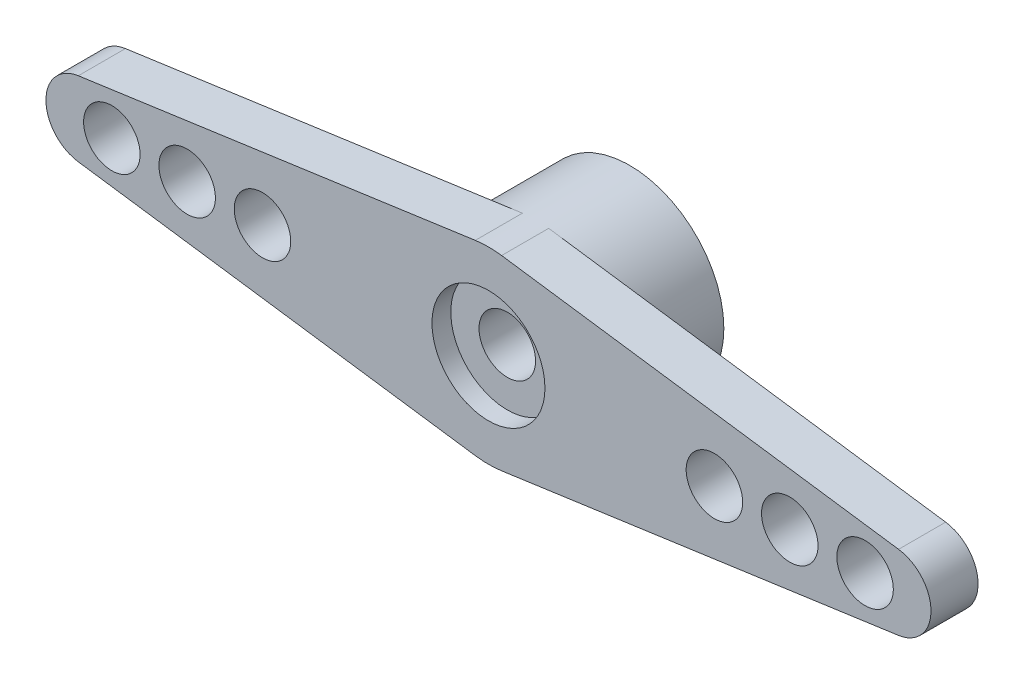
SolidWorks part; units mm, degrees
ref_plane "前视基准面" through (0, 0, 0) normal (0, 0, 1) x (1, 0, 0)
ref_plane "上视基准面" through (0, 0, 0) normal (0, 1, 0) x (1, 0, 0)
ref_plane "右视基准面" through (0, 0, 0) normal (1, 0, 0) x (0, 0, -1)
other "Configuration Table"
sketch "草图1" plane through (0, 0, 0) normal (0, 0, 1) x (1, 0, 0)
  line L0 (-25.0915, 0) -> (25.0915, 0) construction
  line L1 (-21.7791, 1.9804) -> (-0.6977, 4.9511)
  line L2 (-21.7791, -1.9804) -> (-0.6977, -4.9511)
  line L3 (0.6977, -4.9511) -> (21.7791, -1.9804)
  line L4 (0.6977, 4.9511) -> (21.7791, 1.9804)
  arc A0 (-0.6977, -4.9511) -> (0.6977, -4.9511) centre (0, 0) ccw
  arc A1 (-21.7791, 1.9804) -> (-21.7791, -1.9804) centre (-21.5, 0) ccw
  arc A2 (21.7791, -1.9804) -> (21.7791, 1.9804) centre (21.5, 0) ccw
  arc A3 (0.6977, 4.9511) -> (-0.6977, 4.9511) centre (0, 0) ccw
  point P6 (0, 0)
  dimension "D1" = 10
  dimension "D2" = 21.5
  dimension "D3" = 21.5
  dimension "D4" = 4
extrude "凸台-拉伸2" add sketch "草图1" along normal blind 2.5
sketch "草图3" plane through (0, 0, 2.5) normal (0, 0, 1) x (1, 0, 0)
  line L0 (-33.4634, 0) -> (33.4634, 0) construction
  circle A0 centre (-12, 0) radius 1.5
  circle A1 centre (-16, 0) radius 1.5
  circle A2 centre (-20, 0) radius 1.5
  circle A3 centre (12, 0) radius 1.5
  circle A4 centre (16, 0) radius 1.5
  circle A5 centre (20, 0) radius 1.5
  point P4 (0, 0)
  dimension "D1" = 3
  dimension "D2" = 12
  dimension "D3" = 16
  dimension "D4" = 20
  dimension "D6" = 16
  dimension "D7" = 20
  dimension "D5" = 12
extrude "切除-拉伸1" cut sketch "草图3" against normal up to next
sketch "草图5" plane through (0, 0, 2.5) normal (0, 0, 1) x (1, 0, 0)
  circle A0 centre (0, 0) radius 5
  dimension "D1" = 10
extrude "凸台-拉伸3" add sketch "草图5" against normal blind 7.5
sketch "草图6" plane through (0, 0, -5) normal (0, 0, -1) x (-1, 0, 0)
  circle A0 centre (0, 0) radius 3
  dimension "D1" = 6
extrude "切除-拉伸2" cut sketch "草图6" against normal blind 3.4
sketch "草图7" plane through (0, 0, -1.6) normal (0, 0, -1) x (-1, 0, 0)
  circle A0 centre (0, 0) radius 1.5
  dimension "D1" = 3
extrude "切除-拉伸3" cut sketch "草图7" against normal through all
sketch "草图8" plane through (0, 0, 2.5) normal (0, 0, 1) x (1, 0, 0)
  circle A0 centre (0, 0) radius 3
  dimension "D1" = 6
extrude "切除-拉伸4" cut sketch "草图8" against normal blind 1
equation "\"、\"=2.5"
equation "\"0.3、\"=10"
